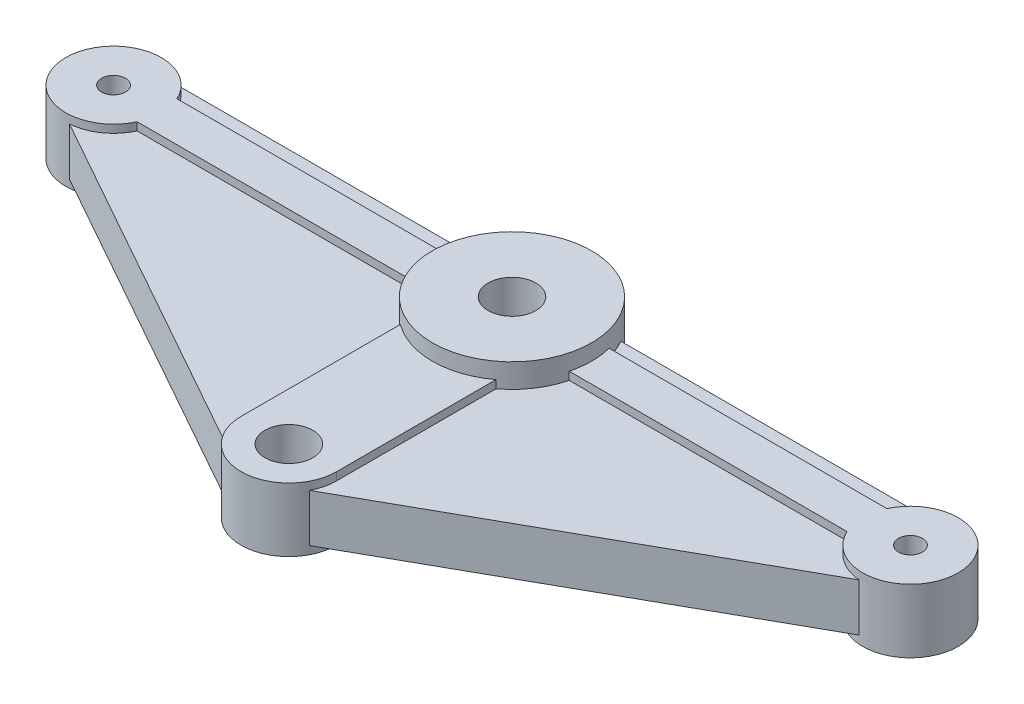
SolidWorks part; units mm, degrees
ref_plane "Front Plane" through (0, 0, 0) normal (0, 0, 1) x (1, 0, 0)
ref_plane "Top Plane" through (0, 0, 0) normal (0, 1, 0) x (1, 0, 0)
ref_plane "Right Plane" through (0, 0, 0) normal (1, 0, 0) x (0, 0, -1)
sketch "Sketch1" plane through (0, 0, 0) normal (0, 1, 0) x (1, 0, 0)
  line L0 (-25, 0) -> (25, 0) construction
  line L1 (0, 0) -> (0, -14) construction
  line L2 (-25, 2.5) -> (25, 2.5)
  line L3 (26.2215, -2.1813) -> (1.2215, -16.1813)
  line L4 (-26.2215, -2.1813) -> (-1.2215, -16.1813)
  circle A0 centre (25, 0) radius 0.75
  circle A1 centre (-25, 0) radius 0.75
  circle A2 centre (0, -14) radius 1.5
  circle A3 centre (0, 0) radius 1.5
  arc A4 (25, 2.5) -> (26.2215, -2.1813) centre (25, 0) cw
  arc A5 (-25, 2.5) -> (-26.2215, -2.1813) centre (-25, 0) ccw
  arc A6 (1.2215, -16.1813) -> (-1.2215, -16.1813) centre (0, -14) cw
  dimension "D2" = 1.5
  dimension "D3" = 3
  dimension "D4" = 3
  dimension "D6" = 2.5
  dimension "D1" = 50
  dimension "D5" = 14
extrude "Extrude1" add sketch "Sketch1" along normal mid plane 3
sketch "Sketch2" plane through (0, 0, 0) normal (0, 1, 0) x (1, 0, 0)
  line L0 (-22.2728, 1.25) -> (-0.8292, 1.25)
  line L1 (-22.2728, -1.25) -> (-3, -1.25)
  line L2 (-3, -1.25) -> (-3, -14)
  line L3 (3, -1.25) -> (3, -14)
  line L4 (3, -1.25) -> (22.2728, -1.25)
  line L5 (0.8292, 1.25) -> (22.2728, 1.25)
  arc A0 (22.2728, -1.25) -> (22.2728, 1.25) centre (25, 0) ccw
  arc A1 (-22.2728, 1.25) -> (-22.2728, -1.25) centre (-25, 0) ccw
  arc A2 (-3, -14) -> (3, -14) centre (0, -14) ccw
  arc A3 (-0.8292, 1.25) -> (0.8292, 1.25) centre (0, 0) ccw
  circle A4 centre (0, 0) radius 1.5 construction
  circle A5 centre (25, 0) radius 0.75
  circle A6 centre (0, -14) radius 1.5
  circle A7 centre (-25, 0) radius 0.75
  circle A8 centre (25, 0) radius 0.75 construction
  circle A9 centre (0, -14) radius 1.5 construction
  circle A10 centre (-25, 0) radius 0.75 construction
  dimension "D1" = 3
  dimension "D2" = 2.5
extrude "Extrude2" add sketch "Sketch2" along normal mid plane 4
sketch "Sketch3" plane through (0, 0, 0) normal (0, 1, 0) x (1, 0, 0)
  circle A0 centre (0, 0) radius 5
  circle A1 centre (0, 0) radius 1.5
  circle A2 centre (0, 0) radius 1.5 construction
  dimension "D1" = 10
extrude "Extrude3" add sketch "Sketch3" along normal mid plane 6
